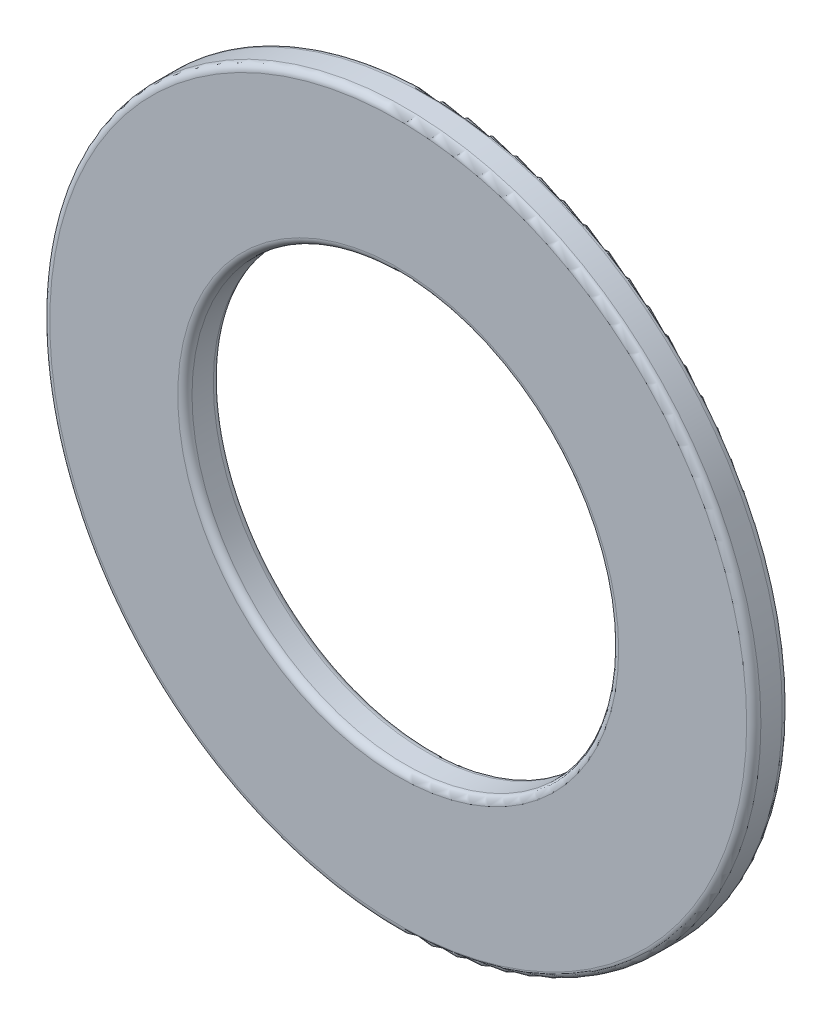
SolidWorks part; units mm, degrees
ref_plane "Piano frontale" through (0, 0, 0) normal (0, 0, 1) x (1, 0, 0)
ref_plane "Piano superiore" through (0, 0, 0) normal (0, 1, 0) x (1, 0, 0)
ref_plane "Piano destro" through (0, 0, 0) normal (1, 0, 0) x (0, 0, -1)
sketch "Schizzo1" plane through (0, 0, 0) normal (0, 0, 1) x (1, 0, 0)
  circle A0 centre (0, 0) radius 5
  circle A1 centre (0, 0) radius 3
extrude "Estrusione-Estrusione1" add sketch "Schizzo1" along normal blind 0.5
fillet "Raccordo1" radius 0.1 4 edges at (3, 0, 0.5) (5, 0, 0.5) (3, 0, 0) (5, 0, 0)
